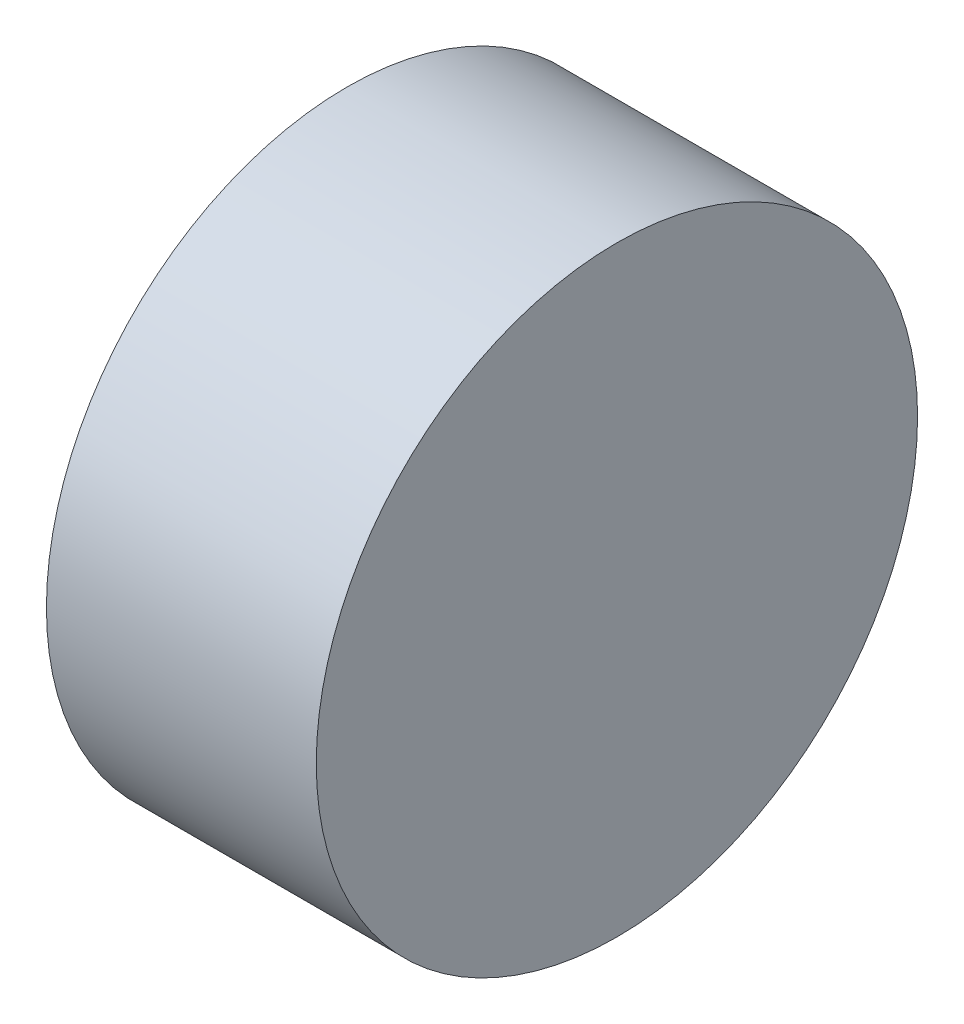
SolidWorks part; units mm, degrees
ref_plane "前视基准面" through (0, 0, 0) normal (0, 0, 1) x (1, 0, 0)
ref_plane "上视基准面" through (0, 0, 0) normal (0, 1, 0) x (1, 0, 0)
ref_plane "右视基准面" through (0, 0, 0) normal (1, 0, 0) x (0, 0, -1)
sketch "草图1" plane through (0, 0, 0) normal (1, 0, 0) x (0, 0, -1)
  circle A0 centre (0, 0) radius 22.2826
extrude "凸台-拉伸1" add sketch "草图1" along normal blind 20
